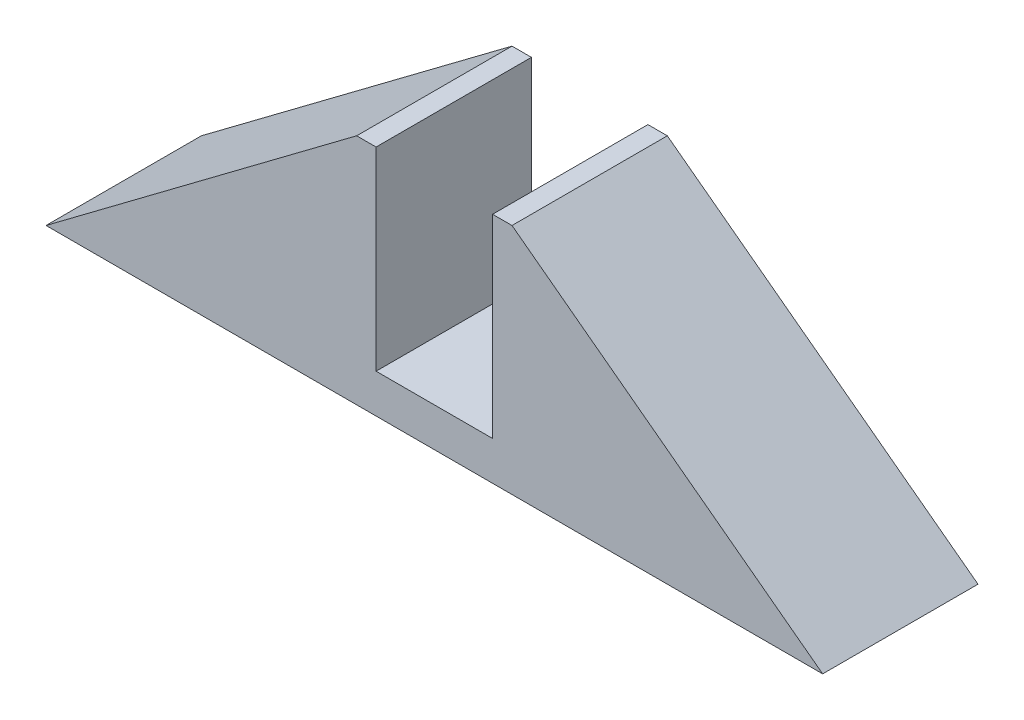
SolidWorks part; units mm, degrees
ref_plane "Alzado" through (0, 0, 0) normal (0, 0, 1) x (1, 0, 0)
ref_plane "Planta" through (0, 0, 0) normal (0, 1, 0) x (1, 0, 0)
ref_plane "Vista lateral" through (0, 0, 0) normal (1, 0, 0) x (0, 0, -1)
sketch "Croquis2" plane through (0, 0, 0) normal (0, 0, 1) x (1, 0, 0)
  line L0 (-10, 15) -> (-50, -15)
  line L1 (-10, 15) -> (10, 15)
  line L3 (-10, -15) -> (10, -15)
  line L5 (-10, 15) -> (10, -15) construction
  line L6 (-10, -15) -> (10, 15) construction
  line L7 (-50, -15) -> (-10, -15)
  line L8 (0, -15) -> (0, 15) construction
  line L9 (50, -15) -> (10, -15)
  line L10 (10, 15) -> (50, -15)
  point P0 (0, 0)
  dimension "D1" = 30
  dimension "D2" = 100
  dimension "D3" = 40
  dimension "D4" = 20
extrude "Saliente-Extruir1" add sketch "Croquis2" along normal mid plane 20
sketch "Croquis3" plane through (0, 0, 10) normal (0, 0, 1) x (1, 0, 0)
  line L1 (-7.5, 15) -> (7.5, 15)
  line L2 (-7.5, 15) -> (-7.5, -10)
  line L3 (-7.5, -10) -> (7.5, -10)
  line L4 (7.5, 15) -> (7.5, -10)
  line L5 (10, 15) -> (-10, 15) construction
  point P6 (0, 15)
  point P7 (0, 15)
  dimension "D1" = 25
  dimension "D2" = 15
extrude "Cortar-Extruir1" cut sketch "Croquis3" against normal blind 20
